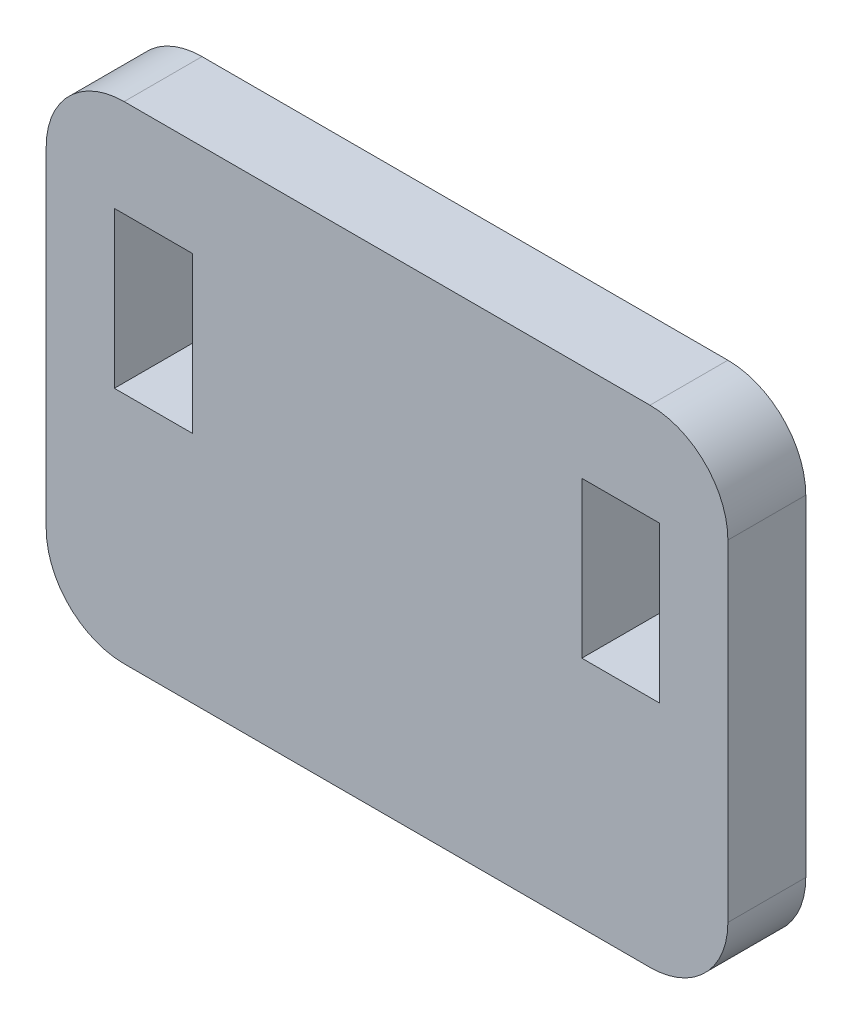
SolidWorks part; units mm, degrees
ref_plane "Front Plane" through (0, 0, 0) normal (0, 0, 1) x (1, 0, 0)
ref_plane "Top Plane" through (0, 0, 0) normal (0, 1, 0) x (1, 0, 0)
ref_plane "Right Plane" through (0, 0, 0) normal (1, 0, 0) x (0, 0, -1)
sketch "Sketch1" plane through (0, 0, 0) normal (0, 0, 1) x (1, 0, 0)
  line L0 (17.5, 25) -> (17.5, 0) construction
  line L1 (4, 0) -> (31, 0)
  line L2 (0, 4) -> (0, 21)
  line L3 (4, 25) -> (31, 25)
  line L4 (35, 4) -> (35, 21)
  line L5 (3.5, 20) -> (7.5, 20)
  line L6 (3.5, 20) -> (3.5, 12)
  line L7 (3.5, 12) -> (7.5, 12)
  line L8 (7.5, 20) -> (7.5, 12)
  line L9 (31.5, 12) -> (27.5, 12)
  line L10 (27.5, 20) -> (27.5, 12)
  line L11 (31.5, 20) -> (27.5, 20)
  line L12 (31.5, 20) -> (31.5, 12)
  arc A0 (31, 0) -> (35, 4) centre (31, 4) ccw
  arc A1 (31, 25) -> (35, 21) centre (31, 21) cw
  arc A2 (0, 21) -> (4, 25) centre (4, 21) cw
  arc A3 (4, 0) -> (0, 4) centre (4, 4) cw
  point P17 (35, 0)
  point P20 (35, 25)
  point P23 (0, 25)
  point P26 (0, 0)
  dimension "D7" = 4
  dimension "D1" = 35
  dimension "D2" = 10
  dimension "D3" = 4
  dimension "D4" = 8
  dimension "D5" = 25
  dimension "D6" = 5
extrude "Boss-Extrude1" add sketch "Sketch1" along normal blind 4
